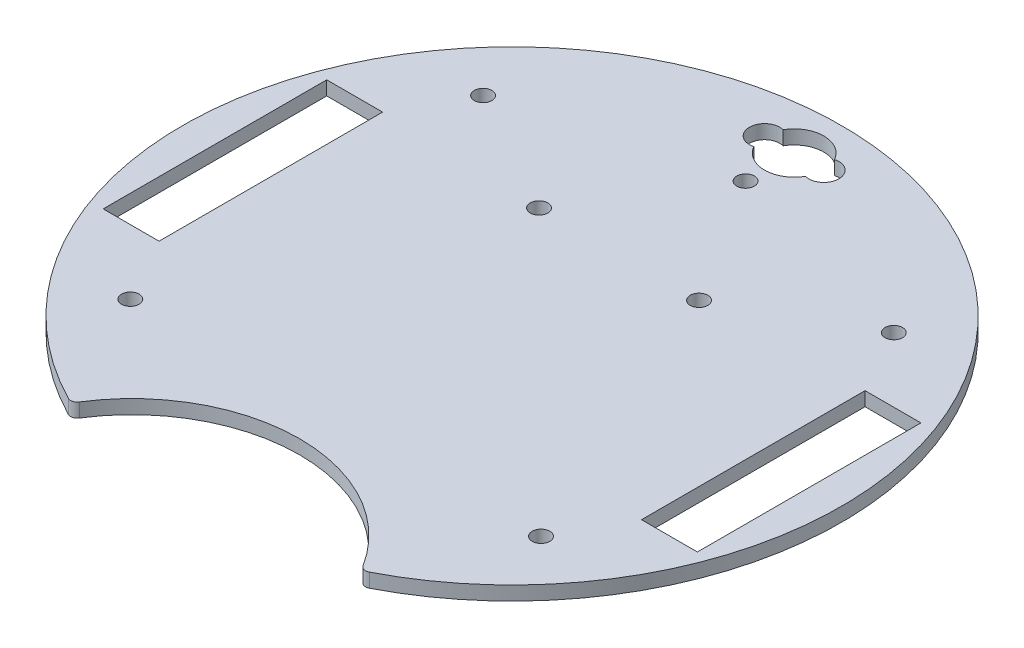
SolidWorks part; units mm, degrees
ref_plane "Front Plane" through (0, 0, 0) normal (0, 0, 1) x (1, 0, 0)
ref_plane "Top Plane" through (0, 0, 0) normal (0, 1, 0) x (1, 0, 0)
ref_plane "Right Plane" through (0, 0, 0) normal (1, 0, 0) x (0, 0, -1)
sketch "Sketch1" plane through (0, 0, 0) normal (0, 1, 0) x (1, 0, 0)
  line L1 (0, 86.2583) -> (0, -96.8543) construction
  line L3 (-32.9956, -67.352) -> (0, -86.402) construction
  line L4 (32.9956, -67.352) -> (0, -86.402) construction
  line L9 (54.8141, -25.4) -> (54.8141, 25.4)
  line L10 (-67.5141, -25.4) -> (-54.8141, -25.4)
  line L11 (-67.5141, -25.4) -> (-67.5141, 25.4)
  line L12 (-67.5141, 25.4) -> (-54.8141, 25.4)
  line L13 (-54.8141, 25.4) -> (-54.8141, -25.4)
  line L14 (67.5141, 25.4) -> (54.8141, 25.4)
  line L15 (67.5141, -25.4) -> (67.5141, 25.4)
  line L16 (67.5141, -25.4) -> (54.8141, -25.4)
  arc A1 (32.2407, -66.1006) -> (-32.2407, -66.1006) centre (0, -86.402) ccw
  arc A2 (34.1948, -66.6358) -> (-34.1948, -66.6358) centre (0, 0) ccw
  arc A3 (5.8576, 67.4236) -> (-5.8539, 67.4301) centre (0, 64.1077) ccw
  arc A4 (-5.8539, 67.4301) -> (-5.8539, 60.7853) centre (-6.731, 64.1077) ccw
  arc A5 (5.8576, 60.7918) -> (5.8576, 67.4236) centre (6.731, 64.1077) ccw
  arc A6 (-5.8539, 60.7853) -> (5.8576, 60.7918) centre (0, 64.1077) ccw
  circle A25 centre (-18.179, 24.3106) radius 2
  circle A38 centre (-46.6637, -40.0812) radius 2
  circle A39 centre (46.6637, -40.0812) radius 2
  circle A40 centre (46.6637, 40.0812) radius 2
  circle A41 centre (-46.6637, 40.0812) radius 2
  arc A42 (-34.1948, -66.6358) -> (-32.2407, -66.1006) centre (-33.51, -65.3013) ccw
  arc A43 (34.1948, -66.6358) -> (32.2407, -66.1006) centre (33.51, -65.3013) cw
  circle A44 centre (-6.731, 64.1077) radius 1.143
  circle A45 centre (6.731, 64.1077) radius 1.143
  circle A47 centre (18.179, 24.3106) radius 2
  circle A48 centre (0, 53.0612) radius 2
  dimension "D3" = 120
  dimension "D15" = 13.462
  dimension "D18" = 2.286
  dimension "D12" = 4
  dimension "D4" = 50.8
  dimension "D5" = 12.7
extrude "Boss-Extrude3" add sketch "Sketch1" along normal blind 3.175 contours A43 A2 A42 A1 A48 A47 A40 A39 A38 L15 L16 L9 L14 L12 L13 L10 L11 A6 A4 A3 A5 A25 A41
sketch "Sketch2" plane through (0, 3.175, 0) normal (0, 1, 0) x (1, 0, 0)
  line L0 (-76.1829, 0) -> (73.6119, 0) construction
  line L1 (0.0037, 29.949) -> (0.0037, -56.3606) construction
  line L2 (-54.8141, 0) -> (30.4838, 0) construction
  line L3 (-54.8141, 25.4) -> (-54.8141, -25.4) construction
  line L5 (0.0037, 57.3767) -> (0.0037, -37.7295) construction
  circle A0 centre (-49.0312, 7.1779) radius 1.5
  circle A1 centre (-49.0312, -7.1779) radius 1.5
  circle A2 centre (-17.2312, 7.1779) radius 1.5
  circle A3 centre (-17.2312, -7.1779) radius 1.5
  circle A4 centre (17.2387, -7.1779) radius 1.5
  circle A5 centre (17.2387, 7.1779) radius 1.5
  circle A6 centre (49.0387, -7.1779) radius 1.5
  circle A7 centre (49.0387, 7.1779) radius 1.5
  arc A8 (-5.8539, 60.7853) -> (5.8576, 60.7918) centre (0, 64.1077) ccw construction
  dimension "D1" = 3
  dimension "D2" = 3
  dimension "D3" = 31.8
